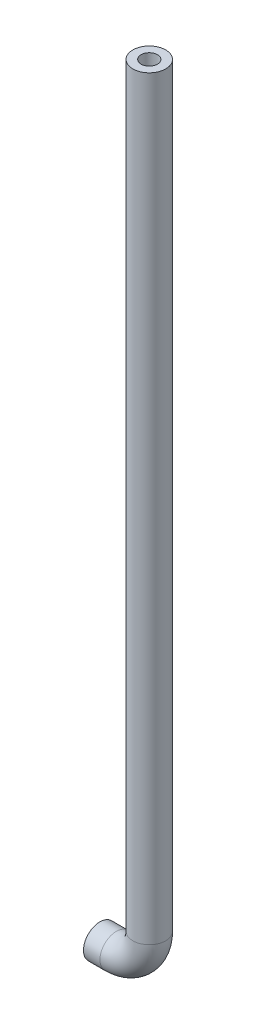
SolidWorks part; units mm, degrees
ref_plane "Front Plane" through (0, 0, 0) normal (0, 0, 1) x (1, 0, 0)
ref_plane "Top Plane" through (0, 0, 0) normal (0, 1, 0) x (1, 0, 0)
ref_plane "Right Plane" through (0, 0, 0) normal (1, 0, 0) x (0, 0, -1)
sketch "Sketch1" plane through (0, 0, 0) normal (0, 0, 1) x (1, 0, 0)
  line L0 (38.1, 608.33) -> (38.1, 25.4)
  line L1 (12.7, 0) -> (0, 0)
  arc A0 (38.1, 25.4) -> (12.7, 0) centre (12.7, 25.4) cw
  point P4 (331.4865, 608.33)
  point P6 (0, 0)
  dimension "D3" = 25.4
  dimension "D1" = 608.33
  dimension "D2" = 12.7
sweep "Sweep1" add path "Sketch1" circular profile diameter 25.4 parameters "D3"=25.4
shell "Shell2" thickness 6.35
